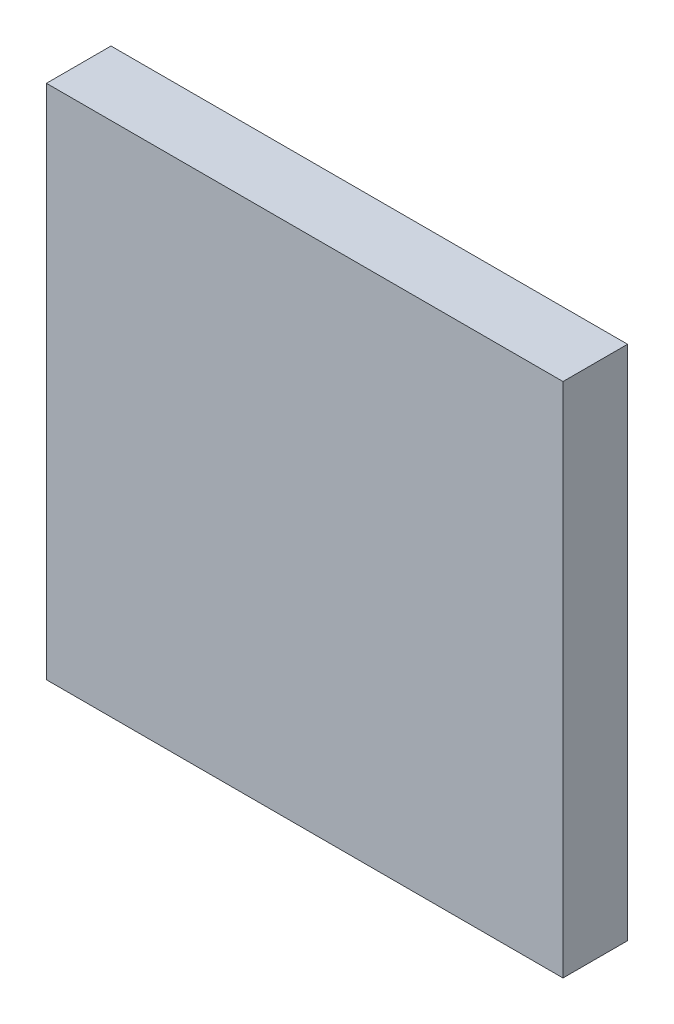
SolidWorks part; units mm, degrees
ref_plane "前视基准面" through (0, 0, 0) normal (0, 0, 1) x (1, 0, 0)
ref_plane "上视基准面" through (0, 0, 0) normal (0, 1, 0) x (1, 0, 0)
ref_plane "右视基准面" through (0, 0, 0) normal (1, 0, 0) x (0, 0, -1)
sketch "草图1" plane through (0, 0, 0) normal (0, 0, 1) x (1, 0, 0)
  line L1 (0, 0) -> (40, 0)
  line L2 (0, 0) -> (0, 40)
  line L3 (0, 40) -> (40, 40)
  line L4 (40, 0) -> (40, 40)
  dimension "D1" = 40
  dimension "D2" = 40
extrude "凸台-拉伸1" add sketch "草图1" along normal blind 5
